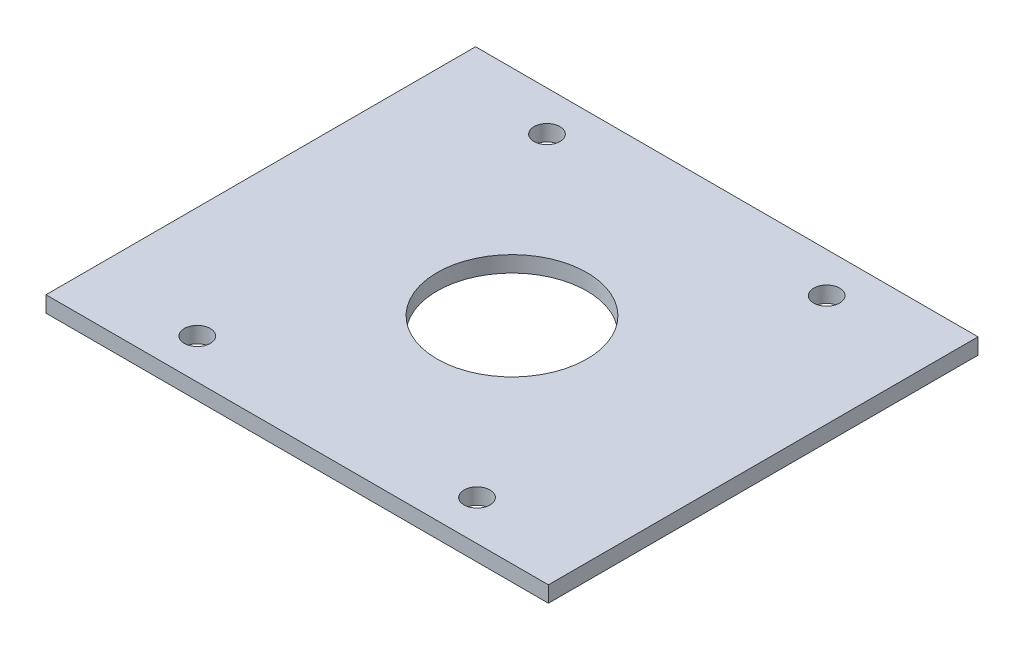
SolidWorks part; units mm, degrees
ref_plane "Front Plane" through (0, 0, 0) normal (0, 0, 1) x (1, 0, 0)
ref_plane "Top Plane" through (0, 0, 0) normal (0, 1, 0) x (1, 0, 0)
ref_plane "Right Plane" through (0, 0, 0) normal (1, 0, 0) x (0, 0, -1)
sketch "Sketch1" plane through (0, 0, 0) normal (0, 1, 0) x (1, 0, 0)
  line L1 (-25.146, 21.5) -> (25.146, 21.5)
  line L2 (-25.146, 21.5) -> (-25.146, -21.5)
  line L3 (-25.146, -21.5) -> (25.146, -21.5)
  line L4 (25.146, 21.5) -> (25.146, -21.5)
  line L5 (-25.146, 21.5) -> (25.146, -21.5) construction
  line L6 (-25.146, -21.5) -> (25.146, 21.5) construction
  circle A0 centre (0, 0) radius 7.5
  circle A1 centre (0, 0) radius 19 construction
  point P0 (0, 0)
  dimension "D3" = 15
  dimension "D4" = 38
  dimension "D1" = 43
  dimension "D2" = 50.292
extrude "Boss-Extrude1" add sketch "Sketch1" along normal blind 1.6
sketch "Sketch2" plane through (0, 0, 0) normal (0, 1, 0) x (1, 0, 0)
  line L1 (0, 0) -> (0, 21.1286) construction
  line L3 (-25.146, 21.5) -> (25.146, 21.5) construction
  line L5 (0, 0) -> (-45.0211, 0) construction
  circle A1 centre (-14, 17.5) radius 1.3
  circle A2 centre (14, 17.5) radius 1.3
  circle A3 centre (14, -17.5) radius 1.3
  circle A4 centre (-14, -17.5) radius 1.3
  dimension "D1" = 2.6
  dimension "D2" = 4
  dimension "D3" = 14
  dimension "D4" = 17.5
extrude "Cut-Extrude3" cut sketch "Sketch2" along normal through all
